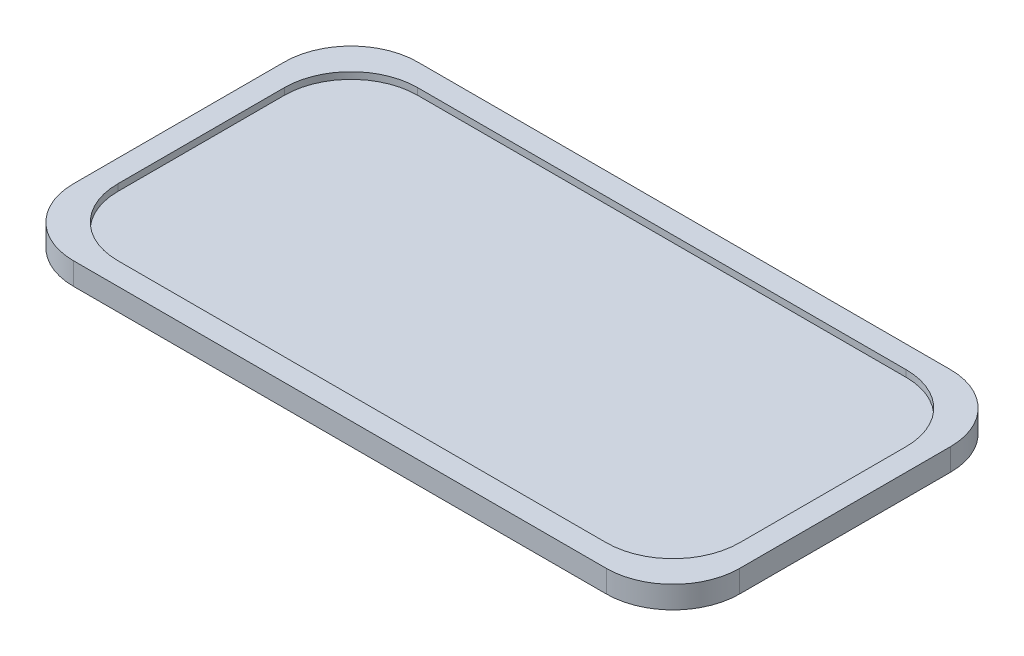
SolidWorks part; units mm, degrees
ref_plane "Front Plane" through (0, 0, 0) normal (0, 0, 1) x (1, 0, 0)
ref_plane "Top Plane" through (0, 0, 0) normal (0, 1, 0) x (1, 0, 0)
ref_plane "Right Plane" through (0, 0, 0) normal (1, 0, 0) x (0, 0, -1)
sketch "Sketch1" plane through (0, 0, 0) normal (0, 1, 0) x (1, 0, 0)
  line L1 (-120, 77.5) -> (120, 77.5)
  line L2 (-150, 47.5) -> (-150, -47.5)
  line L3 (-120, -77.5) -> (120, -77.5)
  line L4 (150, 47.5) -> (150, -47.5)
  line L5 (-150, 77.5) -> (150, -77.5) construction
  line L6 (-150, -77.5) -> (150, 77.5) construction
  arc A0 (150, 47.5) -> (120, 77.5) centre (120, 47.5) ccw
  arc A1 (120, -77.5) -> (150, -47.5) centre (120, -47.5) ccw
  arc A2 (-120, -77.5) -> (-150, -47.5) centre (-120, -47.5) cw
  arc A3 (-150, 47.5) -> (-120, 77.5) centre (-120, 47.5) cw
  point P0 (0, 0)
  dimension "D3" = 30
  dimension "D1" = 155
  dimension "D2" = 300
extrude "Boss-Extrude1" add sketch "Sketch1" along normal blind 10
sketch "Sketch2" plane through (0, 0, 0) normal (0, -1, 0) x (1, 0, 0)
  line L0 (-110, 73.5) -> (110, 73.5)
  line L1 (-110, 67.5) -> (110, 67.5)
  line L2 (-140, 37.5) -> (-140, -37.5)
  line L3 (-110, -67.5) -> (110, -67.5)
  line L4 (140, 37.5) -> (140, -37.5)
  line L5 (-140, 67.5) -> (140, -67.5) construction
  line L6 (-140, -67.5) -> (140, 67.5) construction
  line L7 (146, 37.5) -> (146, -37.5)
  line L8 (-110, -73.5) -> (110, -73.5)
  line L9 (-146, 37.5) -> (-146, -37.5)
  arc A0 (110, -67.5) -> (140, -37.5) centre (110, -37.5) ccw
  arc A1 (140, 37.5) -> (110, 67.5) centre (110, 37.5) ccw
  arc A2 (-110, -67.5) -> (-140, -37.5) centre (-110, -37.5) cw
  arc A3 (-140, 37.5) -> (-110, 67.5) centre (-110, 37.5) cw
  arc A4 (146, 37.5) -> (110, 73.5) centre (110, 37.5) ccw
  arc A5 (110, -73.5) -> (146, -37.5) centre (110, -37.5) ccw
  arc A6 (-110, -73.5) -> (-146, -37.5) centre (-110, -37.5) cw
  arc A7 (-146, 37.5) -> (-110, 73.5) centre (-110, 37.5) cw
  point P0 (0, 0)
  dimension "D3" = 30
  dimension "D1" = 135
  dimension "D2" = 280
  dimension "D4" = 6
extrude "Cut-Extrude1" cut sketch "Sketch2" against normal blind 5
sketch "Sketch3" plane through (0, 10, 0) normal (0, 1, 0) x (1, 0, 0)
  line L1 (-110, 67.5) -> (110, 67.5)
  line L2 (-140, 37.5) -> (-140, -37.5)
  line L3 (-110, -67.5) -> (110, -67.5)
  line L4 (140, 37.5) -> (140, -37.5)
  line L5 (-140, 67.5) -> (140, -67.5) construction
  line L6 (-140, -67.5) -> (140, 67.5) construction
  arc A0 (140, 37.5) -> (110, 67.5) centre (110, 37.5) ccw
  arc A1 (110, -67.5) -> (140, -37.5) centre (110, -37.5) ccw
  arc A2 (-110, -67.5) -> (-140, -37.5) centre (-110, -37.5) cw
  arc A3 (-140, 37.5) -> (-110, 67.5) centre (-110, 37.5) cw
  point P0 (0, 0)
  dimension "D3" = 30
  dimension "D1" = 135
  dimension "D2" = 280
extrude "Cut-Extrude2" cut sketch "Sketch3" against normal blind 3
